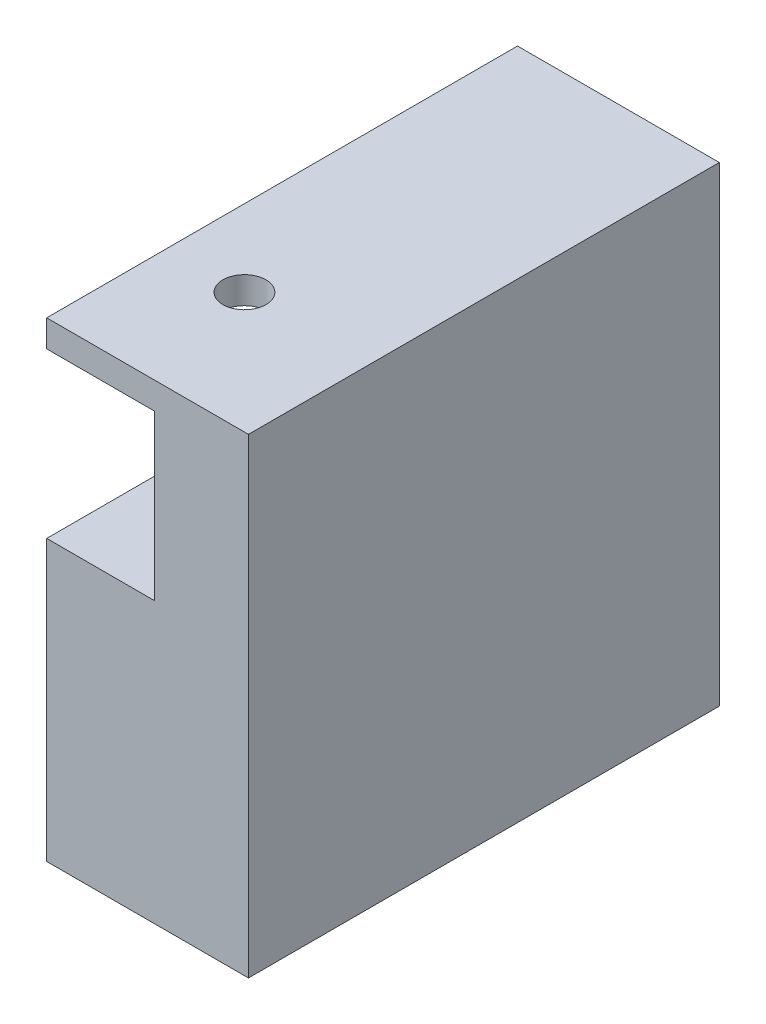
SolidWorks part; units mm, degrees
material "6061-T6 Al"
ref_plane "Front" through (0, 0, 0) normal (0, 0, 1) x (1, 0, 0)
ref_plane "Top" through (0, 0, 0) normal (0, 1, 0) x (1, 0, 0)
ref_plane "Right" through (0, 0, 0) normal (1, 0, 0) x (0, 0, -1)
sketch "Sketch1" plane through (0, 0, 0) normal (0, 1, 0) x (1, 0, 0)
  line L1 (-7.5, 17.5) -> (7.5, 17.5)
  line L2 (-7.5, 17.5) -> (-7.5, -17.5)
  line L3 (-7.5, -17.5) -> (7.5, -17.5)
  line L4 (7.5, 17.5) -> (7.5, -17.5)
  line L5 (-7.5, 17.5) -> (7.5, -17.5) construction
  line L6 (-7.5, -17.5) -> (7.5, 17.5) construction
  point P0 (0, 0)
  dimension "D1" = 35
  dimension "D2" = 15
extrude "Boss-Extrude1" add sketch "Sketch1" along normal blind 35
sketch "Sketch2" plane through (0, 35, 0) normal (0, 1, 0) x (1, 0, 0)
  line L0 (2.5, 17.5) -> (2.5, -17.5)
  line L1 (7.5, 17.5) -> (-7.5, 17.5) construction
  line L2 (-7.5, -17.5) -> (7.5, -17.5) construction
  line L3 (2.5, -17.5) -> (0.3, -17.5)
  line L4 (0.3, -17.5) -> (0.3, -3.35)
  line L5 (0.3, -3.35) -> (-7.5, -3.35)
  line L6 (-7.5, 17.5) -> (-7.5, -17.5) construction
  line L7 (-7.5, -3.35) -> (-7.5, 3.35)
  line L8 (-7.5, 3.35) -> (0.3, 3.35)
  line L9 (0.3, 3.35) -> (0.3, 17.5)
  line L10 (0.3, 17.5) -> (2.5, 17.5)
  line L11 (7.5, -17.5) -> (7.5, 17.5) construction
  dimension "D1" = 6.7
  dimension "D2" = 2.2
  dimension "D3" = 5
extrude "Cut-Extrude1" [suppressed] cut sketch "Sketch2" against normal blind 8
sketch "Sketch3" plane through (0, 0, 17.5) normal (0, 0, 1) x (1, 0, 0)
  line L0 (-7.5, 35) -> (-7.5, 0) construction
  line L1 (-7.5, 33) -> (0.5, 33)
  line L2 (-7.5, 33) -> (-7.5, 20.8)
  line L3 (-7.5, 20.8) -> (0.5, 20.8)
  line L4 (0.5, 33) -> (0.5, 20.8)
  line L5 (-7.5, 35) -> (7.5, 35) construction
  dimension "D1" = 12.2
  dimension "D2" = 2
  dimension "D3" = 8
extrude "Cut-Extrude2" cut sketch "Sketch3" against normal blind 18
sketch "Sketch4" plane through (0, 35, 0) normal (0, 1, 0) x (1, 0, 0)
  line L0 (-7.5, -17.5) -> (7.5, -17.5) construction
  line L3 (0.5, 0.5) -> (0.5, -17.5) construction
  circle A0 centre (-1.8, -8.5) radius 1.6
  dimension "D3" = 3.2
  dimension "D1" = 9
  dimension "D2" = 2.3
extrude "Cut-Extrude3" cut sketch "Sketch4" against normal blind 8
